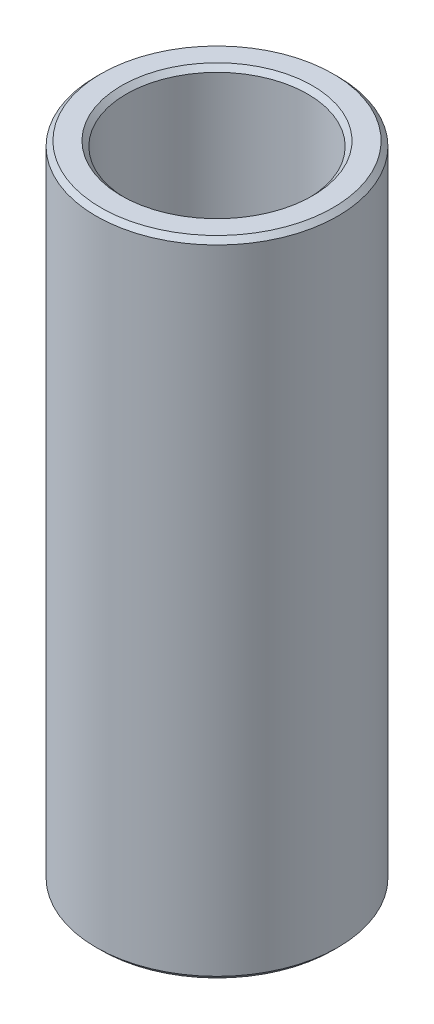
SolidWorks part; units mm, degrees
ref_plane "Front Plane" through (0, 0, 0) normal (0, 0, 1) x (1, 0, 0)
ref_plane "Top Plane" through (0, 0, 0) normal (0, 1, 0) x (1, 0, 0)
ref_plane "Right Plane" through (0, 0, 0) normal (1, 0, 0) x (0, 0, -1)
sketch "Sketch1" plane through (0, 0, 0) normal (0, 0, 1) x (1, 0, 0)
  line L0 (4.7625, 131.7624) -> (4.7625, 165.5386)
  line L1 (4.7625, 165.5386) -> (6.35, 165.5386)
  line L2 (6.35, 165.5386) -> (6.35, 131.7624)
  line L3 (6.35, 131.7624) -> (4.7625, 131.7624)
  line L4 (120.0875, 140.4936) -> (10.0875, 140.4936) construction
  line L6 (0, 122.2374) -> (0, 175.0636) construction
  dimension "D1" = 9.525
  dimension "D2" = 9.525
  dimension "D3" = 12.7
  dimension "D4" = 9.525
revolve "Revolve1" add sketch "Sketch1" angle 360 about L6
chamfer "Chamfer1" distance 0.254 angle 45 4 edges at (6.35, 165.5386, 0) (4.7625, 165.5386, 0) (4.7625, 131.7624, 0) (6.35, 131.7624, 0)
equation "\"D4@Sketch1\"=\"D1@Sketch1\""
